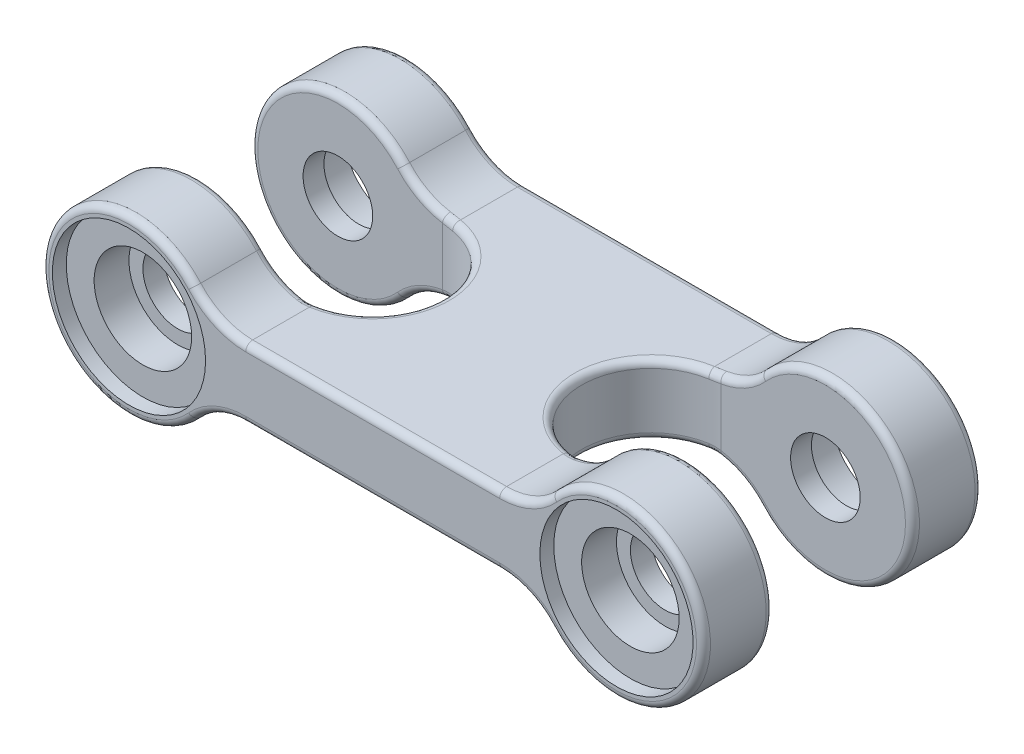
SolidWorks part; units mm, degrees
ref_plane "Front Plane" through (0, 0, 0) normal (0, 0, 1) x (1, 0, 0)
ref_plane "Top Plane" through (0, 0, 0) normal (0, 1, 0) x (1, 0, 0)
ref_plane "Right Plane" through (0, 0, 0) normal (1, 0, 0) x (0, 0, -1)
sketch "Sketch1" plane through (0, 0, 0) normal (0, 0, 1) x (1, 0, 0)
  line L0 (0, 5) -> (0, -5) construction
  line L1 (-18.2295, 5) -> (18.2295, 5)
  line L3 (-18.2295, -5) -> (18.2295, -5)
  line L5 (-35, 0) -> (35, 0) construction
  arc A0 (-25.6831, 8.3333) -> (-25.6831, -8.3333) centre (-35, 0) ccw
  arc A1 (25.6831, -8.3333) -> (25.6831, 8.3333) centre (35, 0) ccw
  arc A2 (-25.6831, -8.3333) -> (-18.2295, -5) centre (-18.2295, -15) cw
  arc A3 (18.2295, -5) -> (25.6831, -8.3333) centre (18.2295, -15) cw
  arc A4 (18.2295, 5) -> (25.6831, 8.3333) centre (18.2295, 15) ccw
  arc A5 (-18.2295, 5) -> (-25.6831, 8.3333) centre (-18.2295, 15) cw
  dimension "D1" = 25
  dimension "D4" = 10
  dimension "D2" = 70
  dimension "D3" = 10
extrude "Boss-Extrude1" add sketch "Sketch1" along normal mid plane 40
sketch "Sketch2" plane through (0, 0, 0) normal (0, 1, 0) x (1, 0, 0)
  line L0 (-47.5, 20) -> (-47.5, -20) construction
  line L1 (-47.5, 10) -> (-20, 10)
  line L2 (-47.5, 10) -> (-47.5, -10)
  line L3 (-47.5, -10) -> (-20, -10)
  line L4 (0, 24.7796) -> (0, -25.8677) construction
  line L5 (47.5, -10) -> (20, -10)
  line L6 (47.5, 10) -> (47.5, -10)
  line L7 (47.5, 10) -> (20, 10)
  arc A0 (-20, -10) -> (-20, 10) centre (-20, 0) ccw
  arc A1 (20, -10) -> (20, 10) centre (20, 0) cw
  dimension "D1" = 20
  dimension "D2" = 20
extrude "Cut-Extrude1" cut sketch "Sketch2" against normal through all and the other way through all
sketch "Sketch3" plane through (0, 0, 20) normal (0, 0, 1) x (1, 0, 0)
  circle A0 centre (-35, 0) radius 5
  dimension "D1" = 10
extrude "Cut-Extrude2" cut sketch "Sketch3" against normal up to next (10 mm away)
sketch "Sketch4" plane through (0, 0, 20) normal (0, 0, 1) x (1, 0, 0)
  circle A0 centre (-35, 0) radius 7
  circle A1 centre (-35, 0) radius 5 construction
  dimension "D1" = 2
extrude "Cut-Extrude3" cut sketch "Sketch4" against normal blind 7
sketch "Sketch5" plane through (0, 0, 20) normal (0, 0, 1) x (1, 0, 0)
  circle A0 centre (-35, 0) radius 11
  circle A1 centre (-35, 0) radius 7 construction
  dimension "D1" = 4
extrude "Cut-Extrude4" cut sketch "Sketch5" against normal blind 2
mirror "Mirror1" about plane through (0, 0, 0) normal (1, 0, 0) of "Cut-Extrude2", "Cut-Extrude3", "Cut-Extrude4"
mirror "Mirror2" about plane through (0, 0, 0) normal (0, 0, 1) of "Mirror1", "Cut-Extrude2", "Cut-Extrude3", "Cut-Extrude4"
fillet "Fillet1" radius 1 40 edges at (22.312, 5.8713, 20) (47.5, 0, 20) (22.312, -5.8713, 20) (0, -5, 20) (-22.312, -5.8713, 20) (-47.5, 0, 20) (-22.312, 5.8713, 20) (-23.1072, 6.2703, -10) (-47.5, 0, -10) (-23.1072, -6.2703, -10) (-10, -5, 0) (-23.1072, -6.2703, 10) (-47.5, 0, 10) (-23.1072, 6.2703, 10) (23.1072, 6.2703, 10) (47.5, 0, 10) (23.1072, -6.2703, 10) (10, -5, 0) (23.1072, -6.2703, -10) (47.5, 0, -10) (23.1072, 6.2703, -10) (22.312, 5.8713, -20) (47.5, 0, -20) (22.312, -5.8713, -20) (0, -5, -20) (-22.312, -5.8713, -20) (-47.5, 0, -20) (-22.312, 5.8713, -20) (0, 5, 20) (-10, 5, 0) (10, 5, 0) (0, 5, -20)
